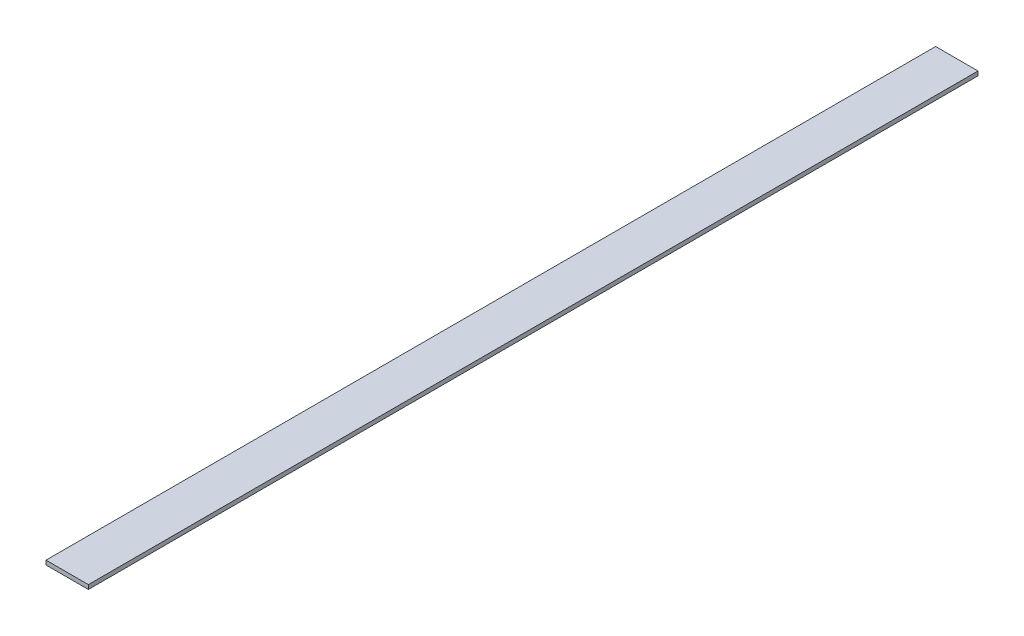
SolidWorks part; units mm, degrees
ref_plane "Front Plane" through (0, 0, 0) normal (0, 0, 1) x (1, 0, 0)
ref_plane "Top Plane" through (0, 0, 0) normal (0, 1, 0) x (1, 0, 0)
ref_plane "Right Plane" through (0, 0, 0) normal (1, 0, 0) x (0, 0, -1)
sketch "Sketch1" plane through (0, 0, 0) normal (0, 1, 0) x (1, 0, 0)
  line L0 (0, 0) -> (0, 1066.8)
  line L1 (0, 1066.8) -> (-50.8, 1066.8)
  line L2 (-50.8, 1066.8) -> (-50.8, 0)
  line L3 (-50.8, 0) -> (0, 0)
  dimension "D1" = 50.8
  dimension "D2" = 1066.8
extrude "Boss-Extrude1" add sketch "Sketch1" along normal blind 5.08
